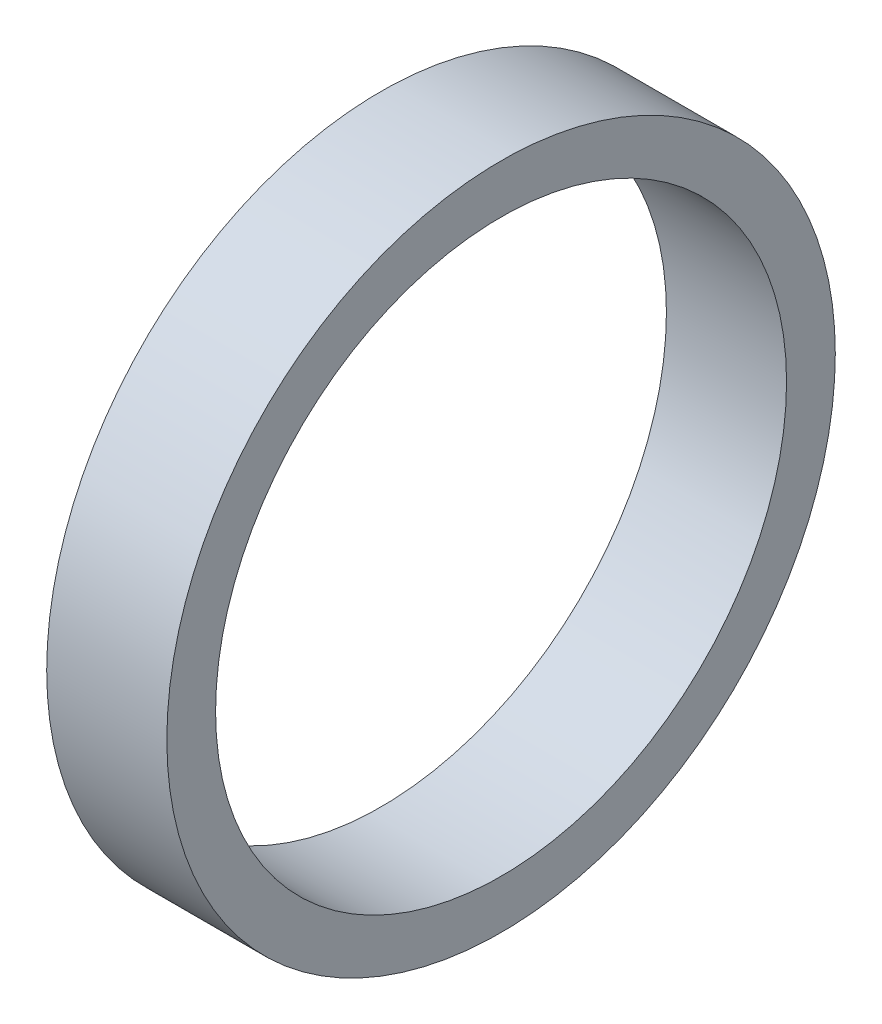
SolidWorks part; units mm, degrees
ref_plane "Ön Düzlem" through (0, 0, 0) normal (0, 0, 1) x (1, 0, 0)
ref_plane "Üst Düzlem" through (0, 0, 0) normal (0, 1, 0) x (1, 0, 0)
ref_plane "Sağ Düzlem" through (0, 0, 0) normal (1, 0, 0) x (0, 0, -1)
sketch "Sketch1" plane through (0, 0, 0) normal (1, 0, 0) x (0, 0, -1)
  circle A0 centre (0, 0) radius 15.375
  circle A1 centre (0, 0) radius 18
  dimension "D1" = 30.75
  dimension "D2" = 36
extrude "Boss-Extrude1" add sketch "Sketch1" along normal blind 6.47
